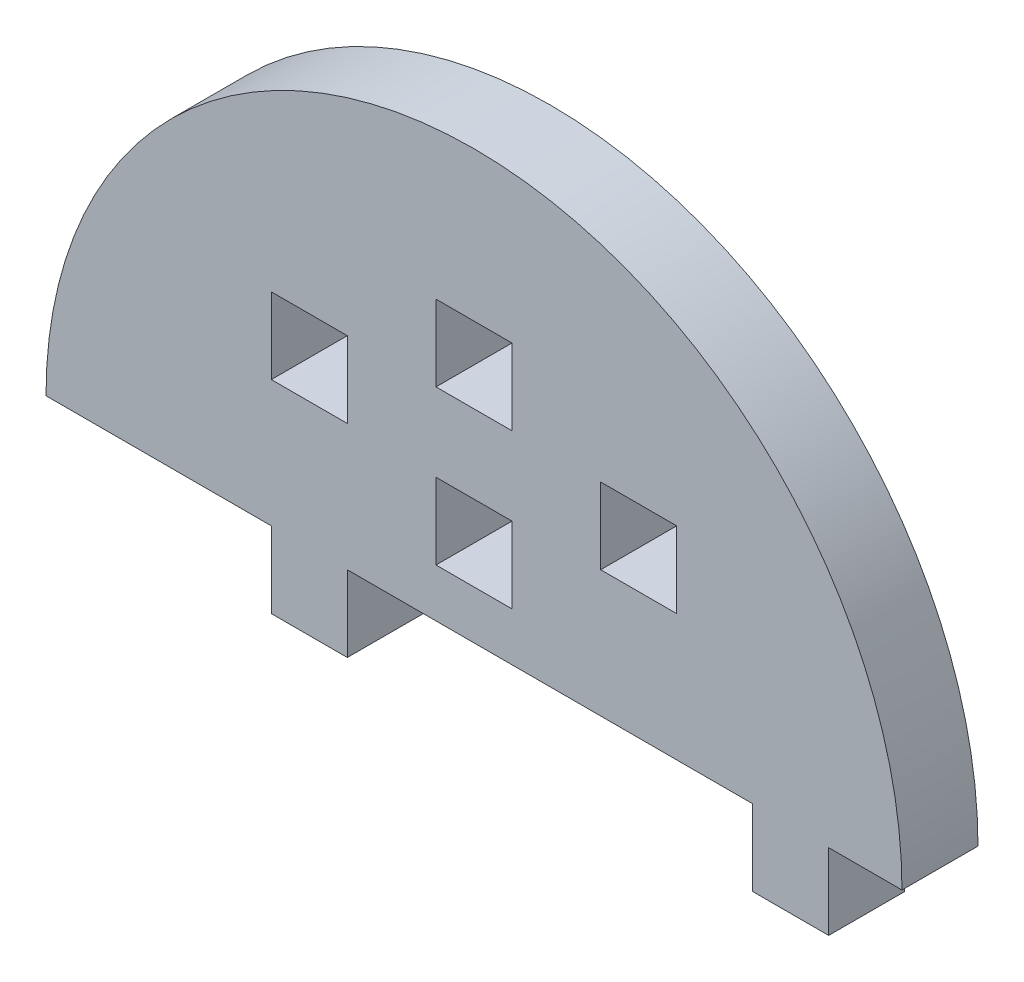
SolidWorks part; units mm, degrees
ref_plane "Front Plane" through (0, 0, 0) normal (0, 0, 1) x (1, 0, 0)
ref_plane "Top Plane" through (0, 0, 0) normal (0, 1, 0) x (1, 0, 0)
ref_plane "Right Plane" through (0, 0, 0) normal (1, 0, 0) x (0, 0, -1)
sketch "Model" plane through (0, 0, 0) normal (0, 0, 1) x (1, 0, 0)
  line L0 (3958.2734, 1148.7047) -> (3964.2734, 1148.7047)
  line L1 (3964.2734, 1148.7047) -> (3964.2734, 1142.7047)
  line L2 (3964.2734, 1142.7047) -> (3958.2734, 1142.7047)
  line L3 (3958.2734, 1142.7047) -> (3958.2734, 1148.7047)
  line L4 (3938.2734, 1148.7047) -> (3932.2734, 1148.7047)
  line L5 (3932.2734, 1148.7047) -> (3932.2734, 1142.7047)
  line L6 (3932.2734, 1142.7047) -> (3938.2734, 1142.7047)
  line L7 (3938.2734, 1142.7047) -> (3938.2734, 1148.7047)
  line L8 (3945.2734, 1154.7047) -> (3951.2734, 1154.7047)
  line L9 (3951.2734, 1154.7047) -> (3951.2734, 1148.7047)
  line L10 (3951.2734, 1148.7047) -> (3945.2734, 1148.7047)
  line L11 (3945.2734, 1148.7047) -> (3945.2734, 1154.7047)
  line L12 (3945.2734, 1136.5292) -> (3951.2734, 1136.5292)
  line L13 (3951.2734, 1136.5292) -> (3951.2734, 1142.5292)
  line L14 (3951.2734, 1142.5292) -> (3945.2734, 1142.5292)
  line L15 (3945.2734, 1142.5292) -> (3945.2734, 1136.5292)
  line L16 (3970.2734, 1132.7047) -> (3970.2734, 1126.7047)
  line L17 (3970.2734, 1126.7047) -> (3976.2734, 1126.7047)
  line L18 (3976.2734, 1126.7047) -> (3976.2734, 1132.7047)
  line L19 (3938.2734, 1132.7047) -> (3938.2734, 1126.7047)
  line L20 (3938.2734, 1126.7047) -> (3932.2734, 1126.7047)
  line L21 (3932.2734, 1126.7047) -> (3932.2734, 1132.7047)
  line L22 (3914.4877, 1132.7047) -> (3932.2734, 1132.7047)
  line L23 (3938.2734, 1132.7047) -> (3970.2734, 1132.7047)
  line L24 (3976.2734, 1132.7047) -> (3982.0591, 1132.7047)
  arc A0 (3982.0591, 1132.7047) -> (3914.4877, 1132.7047) centre (3948.2734, 1132.7047) ccw
extrude "Boss-Extrude1" add sketch "Model" along normal blind 6 contours L6 L7 L4 L5 | L14 L15 L12 L13 | L3 L2 L1 L0 | A0 L22 L21 L20 L19 L23 L16 L17 L18 L24 | L11 L8 L9 L10
